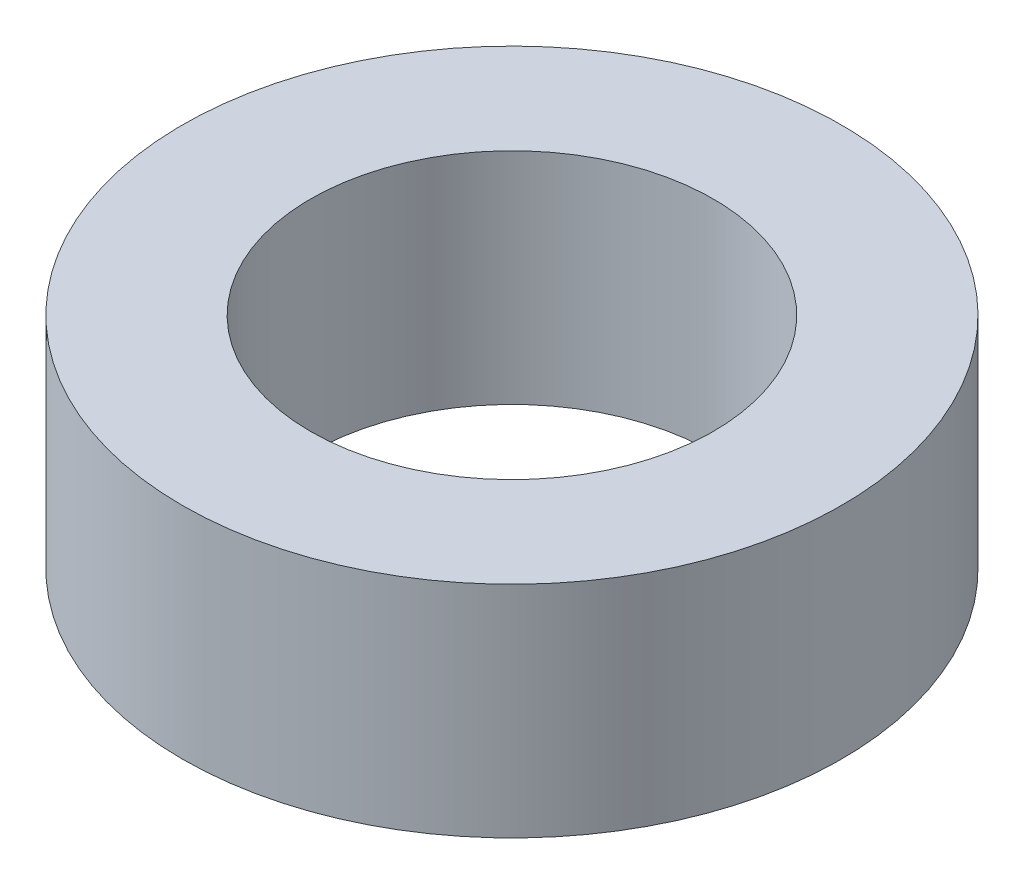
SolidWorks part; units mm, degrees
ref_plane "Front Plane" through (0, 0, 0) normal (0, 0, 1) x (1, 0, 0)
ref_plane "Top Plane" through (0, 0, 0) normal (0, 1, 0) x (1, 0, 0)
ref_plane "Right Plane" through (0, 0, 0) normal (1, 0, 0) x (0, 0, -1)
sketch "Sketch1" plane through (0, 0, 0) normal (0, 1, 0) x (1, 0, 0)
  circle A0 centre (0, 0) radius 2.75
  circle A1 centre (0, 0) radius 4.5
  dimension "D1" = 5.5
  dimension "D2" = 9
extrude "Boss-Extrude1" add sketch "Sketch1" along normal blind 3
